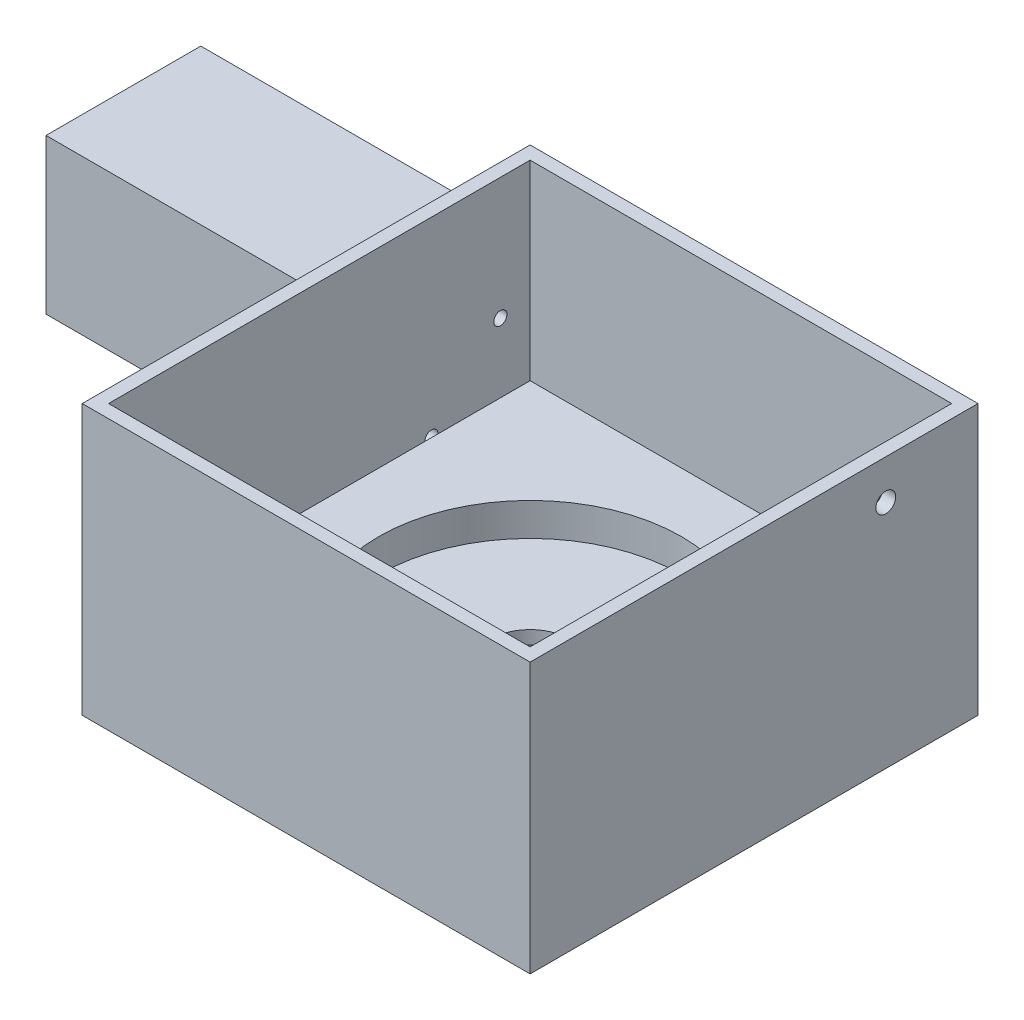
SolidWorks part; units mm, degrees
ref_plane "Front Plane" through (0, 0, 0) normal (0, 0, 1) x (1, 0, 0)
ref_plane "Top Plane" through (0, 0, 0) normal (0, 1, 0) x (1, 0, 0)
ref_plane "Right Plane" through (0, 0, 0) normal (1, 0, 0) x (0, 0, -1)
sketch "Sketch1" plane through (0, 0, 0) normal (0, 1, 0) x (1, 0, 0)
  line L1 (-34, -34) -> (34, -34)
  line L2 (-34, -34) -> (-34, 34)
  line L3 (-34, 34) -> (34, 34)
  line L4 (34, -34) -> (34, 34)
  line L5 (-34, -34) -> (34, 34) construction
  line L6 (-34, 34) -> (34, -34) construction
  point P0 (0, 0)
  dimension "D1" = 68
extrude "Boss-Extrude1" add sketch "Sketch1" along normal blind 41
sketch "Sketch2" plane through (0, 0, 0) normal (0, 1, 0) x (1, 0, 0)
  line L1 (-32, -32) -> (32, -32)
  line L2 (-32, -32) -> (-32, 32)
  line L3 (-32, 32) -> (32, 32)
  line L4 (32, -32) -> (32, 32)
  line L5 (-32, -32) -> (32, 32) construction
  line L6 (-32, 32) -> (32, -32) construction
  point P0 (0, 0)
  dimension "D1" = 64
extrude "Cut-Extrude1" cut sketch "Sketch2" against normal blind 29 from surface at 41 starting at face at (0, 41, 0)
sketch "Sketch3" plane through (0, 0, 0) normal (0, 1, 0) x (1, 0, 0)
  circle A0 centre (0, 0) radius 23
  dimension "D1" = 46
extrude "Cut-Extrude4" cut sketch "Sketch3" against normal blind 5 from surface at 12 starting at face at (0, 12, 0)
sketch "Sketch4" plane through (0, 7, 0) normal (0, 1, 0) x (1, 0, 0)
  line L2 (-19.9206, -1.095) -> (-22.9685, -1.2027)
  line L3 (-19.9903, 1.0511) -> (-22.9701, 1.1719)
  line L8 (-21.6098, -7.8752) -> (-12.5558, -4.8686)
  line L9 (-21.6093, 7.8764) -> (-12.6699, 5.1333)
  line L11 (-12.5558, -4.8686) -> (-12.6699, 5.1333)
  arc A0 (-21.6093, 7.8764) -> (-22.9701, 1.1719) centre (0, 0) ccw
  arc A1 (-22.9685, -1.2027) -> (-21.6098, -7.8752) centre (0, 0) ccw
  circle A2 centre (0, 0) radius 23 construction
  arc A10 (-19.9206, -1.095) -> (-19.9903, 1.0511) centre (-16.6259, 0.0862) ccw
sketch "Sketch5" plane through (0, 0, 0) normal (0, 1, 0) x (1, 0, 0)
  circle A0 centre (0, 0) radius 6.05
  dimension "D1" = 12.1
extrude "Cut-Extrude9" cut sketch "Sketch5" against normal through all from surface at 7 starting at face at (0, 7, 23)
sketch "Sketch6" plane through (0, 0, 0) normal (0, -1, 0) x (1, 0, 0)
  circle A0 centre (0, 0) radius 10.5
  dimension "D1" = 21
extrude "Cut-Extrude10" cut sketch "Sketch6" against normal blind 5 from surface at 0 starting at face at (0, 0, 6.05)
sketch "Sketch7" plane through (0, 0, 0) normal (0, -1, 0) x (-1, 0, 0)
  line L0 (-34, 34) -> (34, -34) construction
  line L1 (-34, -34) -> (34, 34) construction
  line L3 (-15, 15) -> (15, 15)
  line L4 (-15, 15) -> (-15, -15)
  line L5 (-15, -15) -> (15, -15)
  line L6 (15, 15) -> (15, -15)
  line L7 (-13, 13) -> (13, 13)
  line L8 (-13, 13) -> (-13, -13)
  line L9 (-13, -13) -> (13, -13)
  line L10 (13, 13) -> (13, -13)
  point P8 (0, 0)
  dimension "D1" = 30
  dimension "D2" = 26
extrude "Cut-Extrude11" cut sketch "Sketch7" against normal blind 2
sketch "Sketch8" plane through (32, 0, 0) normal (-1, 0, 0) x (0, 0, 1)
  line L0 (32, 12) -> (-32, 12) construction
  line L1 (-32, 12) -> (-32, 41) construction
  circle A0 centre (-20, 35) radius 1.5
  dimension "D1" = 3
  dimension "D2" = 23
  dimension "D3" = 12
extrude "Cut-Extrude12" cut sketch "Sketch8" against normal through all
sketch "Sketch9" plane through (-34, 0, 0) normal (-1, 0, 0) x (0, 0, 1)
  line L0 (-34, 29) -> (-10.5, 5.5) construction
  line L1 (-34, 5.5) -> (-10.5, 5.5)
  line L2 (-34, 5.5) -> (-34, 29)
  line L3 (-34, 29) -> (-10.5, 29)
  line L4 (-10.5, 5.5) -> (-10.5, 29)
  line L5 (-10.5, 29) -> (-34, 5.5) construction
  line L6 (-34, 41) -> (-34, 0) construction
  line L7 (-34, 0) -> (34, 0) construction
  circle A0 centre (-22.25, 17.25) radius 5.6
  point P4 (-34, 4.9544)
  point P7 (0, 0)
  point P8 (-34, 5.9304)
  dimension "D2" = 11.2
  dimension "D3" = 5.5
  dimension "D1" = 23.5
extrude "Boss-Extrude4" add sketch "Sketch9" along normal blind 50
sketch "Sketch11" plane through (-84, 0, 0) normal (-1, 0, 0) x (0, 0, 1)
  line L0 (-34, 29) -> (-10.5, 5.5) construction
  line L2 (-34, 5.5) -> (-10.5, 29) construction
  line L3 (-34, 29) -> (-34, 5.5) construction
  circle A2 centre (-27.4826, 22.4826) radius 1
  circle A3 centre (-17.0174, 12.0174) radius 1
  point P4 (0, 0)
  dimension "D1" = 2
  dimension "D2" = 14.8
extrude "Cut-Extrude13" cut sketch "Sketch11" against normal blind 52
